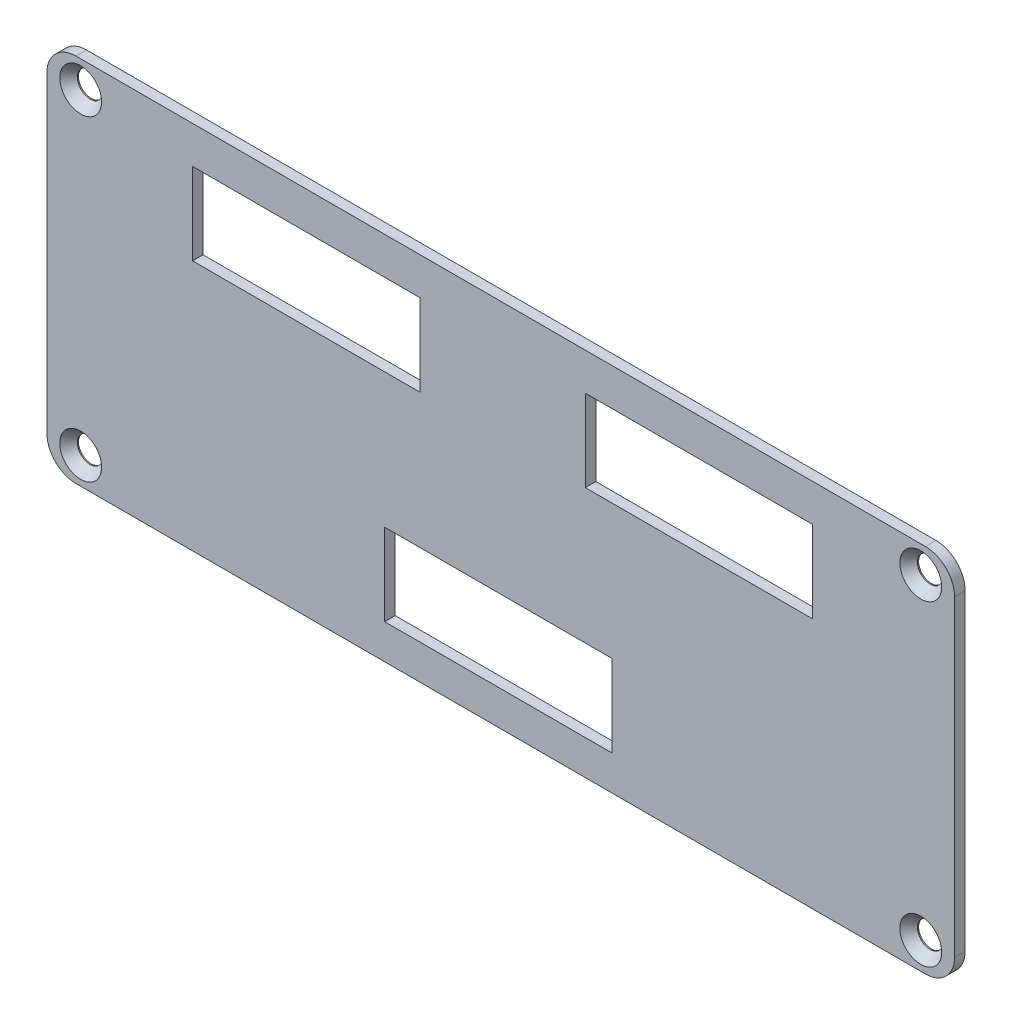
SolidWorks part; units mm, degrees
other "Markup1"
sketch "Sketch3" plane through (0, 0, 0) normal (-0.9973, 0.0561, -0.0476) x (-0.0483, -0.0106, 0.9988)
ref_plane "Front Plane" through (0, 0, 0) normal (0, 0, 1) x (1, 0, 0)
ref_plane "Top Plane" through (0, 0, 0) normal (0, 1, 0) x (1, 0, 0)
ref_plane "Right Plane" through (0, 0, 0) normal (1, 0, 0) x (0, 0, -1)
sketch "Sketch1" plane through (0, 0, 0) normal (0, 0, 1) x (1, 0, 0)
  line L1 (0, 0) -> (124.8, 0)
  line L2 (0, 0) -> (0, -50.9)
  line L3 (0, -50.9) -> (124.8, -50.9)
  line L4 (124.8, 0) -> (124.8, -50.9)
  dimension "D1" = 124.8
  dimension "D2" = 50.9
extrude "Boss-Extrude1" add sketch "Sketch1" along normal blind 1.45
hole_wizard "CSK for M3.5 Flat Head Machine Screw1" positions "3DSketch1" profile "Sketch2" countersink size "M3.5" standard "ANSI Metric" end condition through all
sketch3d "3DSketch1"
  line L0 (124.8, 0, 1.45) -> (0, 0, 1.45) construction
  line L2 (124.8, -50.9, 1.45) -> (124.8, 0, 1.45) construction
  point P0 (4.65, -3.7, 1.45)
  point P2 (120.15, -3.7, 1.45)
  point P4 (120.15, -47.2, 1.45)
  point P6 (4.65, -47.2, 1.45)
  dimension "D3" = 3.7
  dimension "D1" = 115.5
  dimension "D2" = 43.5
  dimension "D4" = 4.65
sketch "Sketch2" plane through (4.65, -3.7, 1.45) normal (1, 0, 0) x (0, -1, 0)
  line L0 (0, 0) -> (0, 1.45)
  line L1 (0, 1.45) -> (1.75, 1.45)
  line L2 (1.75, 1.45) -> (1.75, 1.2942)
  line L3 (1.75, 1.2942) -> (2.875, 0)
  line L5 (2.875, 0) -> (0, 0)
  line L6 (-1.75, 1.2942) -> (-2.875, 0) construction
  line L11 (0, -6.35) -> (0, 107.95) construction
  dimension "Thru Hole Dia." = 3.5
  dimension "Thru Hole Depth" = 1.45
  dimension "Near C'Sink Dia." = 5.75
  dimension "Near C'Sink Angle" = 82
fillet "Fillet2" radius 4 4 edges at (0, 0, 0.725) (124.8, 0, 0.725) (124.8, -50.9, 0.725) (0, -50.9, 0.725)
sketch "Sketch4" plane through (0, 0, 0) normal (0, 0, 1) x (1, 0, 0)
  line L1 (20.026, -5.125) -> (51.276, -5.125)
  line L2 (20.026, -5.125) -> (20.026, -16.375)
  line L3 (20.026, -16.375) -> (51.276, -16.375)
  line L4 (51.276, -5.125) -> (51.276, -16.375)
  line L5 (74.026, -5.125) -> (105.276, -5.125)
  line L6 (74.026, -5.125) -> (74.026, -16.375)
  line L7 (74.026, -16.375) -> (105.276, -16.375)
  line L8 (105.276, -5.125) -> (105.276, -16.375)
  line L9 (46.444, -34.875) -> (77.694, -34.875)
  line L10 (46.444, -34.875) -> (46.444, -46.125)
  line L11 (46.444, -46.125) -> (77.694, -46.125)
  line L12 (77.694, -34.875) -> (77.694, -46.125)
  line L17 (0, 0) -> (124.8, 0)
  line L18 (0, 0) -> (0, -50.9)
  line L19 (0, -50.9) -> (124.8, -50.9)
  line L20 (124.8, 0) -> (124.8, -50.9)
  point P12 (35.651, -5.125)
  point P13 (51.276, -10.75)
  point P14 (35.651, -10.75)
  point P15 (89.651, -10.75)
  point P17 (105.276, -10.75)
  point P18 (89.651, -5.125)
  point P22 (62.069, -40.5)
  point P24 (77.694, -40.5)
  point P25 (62.069, -34.875)
  dimension "D5" = 10.75
  dimension "D6" = 89.651
  dimension "D7" = 40.5
  dimension "D8" = 11.25
  dimension "D1" = 31.25
  dimension "D2" = 50.9
  dimension "D3" = 124.8
  dimension "D4" = 35.651
  dimension "D9" = 62.069
extrude "Cut-Extrude1" cut sketch "Sketch4" along normal up to surface (1.45 mm away) contours L4 L1 L2 L3 | L8 L5 L6 L7 | L12 L9 L10 L11 up to face at (7.525, -3.7, 1.45)
fillet "Fillet3" [suppressed] radius 0.5
equation "\"D3@3DSketch1\"=(50.9-\"D2@3DSketch1\")/2"
equation "\"D4@3DSketch1\"=(124.8-\"D1@3DSketch1\")/2"
